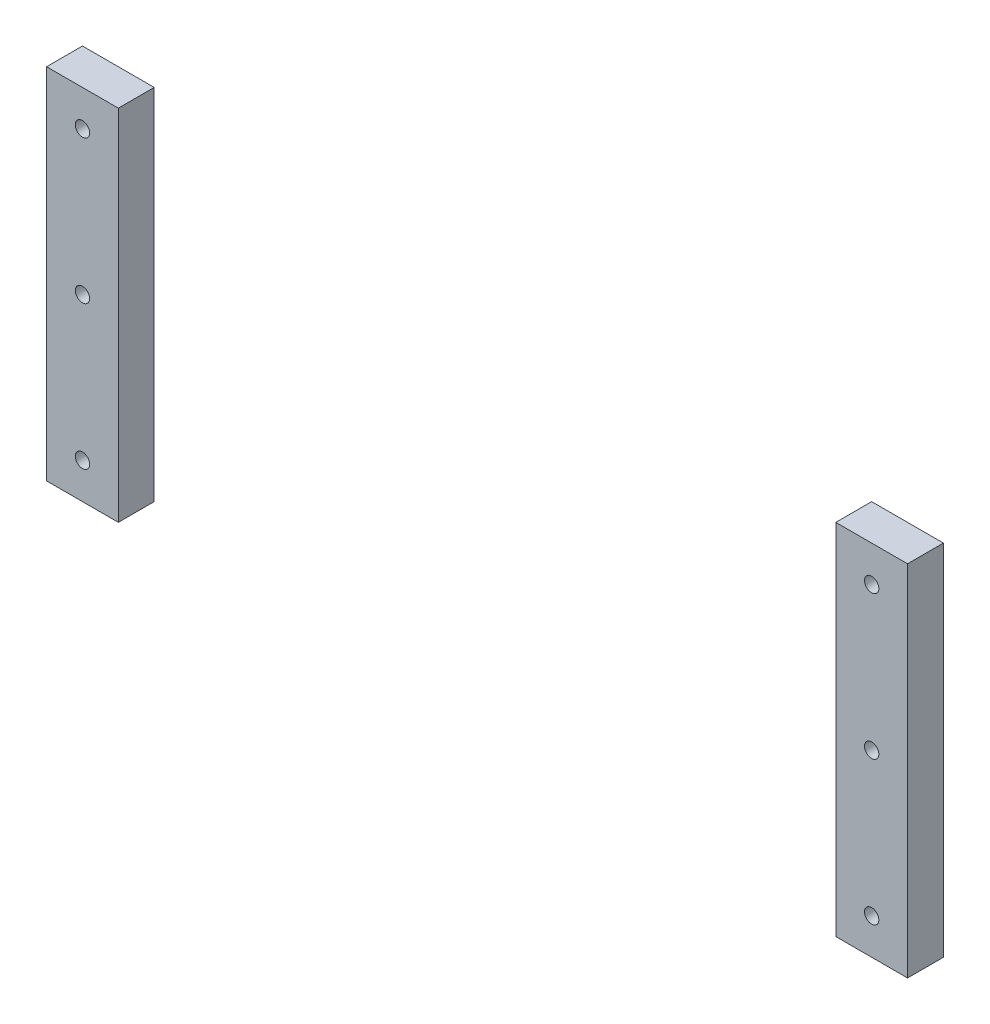
SolidWorks part; units mm, degrees
material "Cast Alloy Steel"
ref_plane "Front Plane" through (0, 0, 0) normal (0, 0, 1) x (1, 0, 0)
ref_plane "Top Plane" through (0, 0, 0) normal (0, 1, 0) x (1, 0, 0)
ref_plane "Right Plane" through (0, 0, 0) normal (1, 0, 0) x (0, 0, -1)
sketch "Sketch1" plane through (0, 0, 0) normal (0, 0, 1) x (1, 0, 0)
  line L0 (200, 0) -> (220, 0)
  line L1 (-20, 0) -> (0, 0)
  line L2 (-20, 0) -> (-20, 100)
  line L3 (-20, 100) -> (0, 100)
  line L4 (0, 0) -> (0, 100)
  line L5 (200, 0) -> (200, 100)
  line L6 (200, 100) -> (220, 100)
  line L7 (220, 0) -> (220, 100)
  line L8 (0, 100) -> (200, 100) construction
  point P4 (0, 0)
  point P11 (0, 0)
  dimension "D1" = 100
  dimension "D2" = 20
  dimension "D3" = 200
extrude "SupportExtrude" add sketch "Sketch1" along normal blind 10
ref_plane "Support Midplane" through (100, 0, 0) normal (1, 0, 0) x (0, 0, -1)
sketch "Sketch2" plane through (0, 0, 10) normal (0, 0, 1) x (1, 0, 0)
  line L0 (-20, 50) -> (0, 50) construction
  line L1 (-20, 100) -> (-20, 0) construction
  line L2 (0, 0) -> (0, 100) construction
  line L3 (-10, 100) -> (-10, 0) construction
  line L4 (0, 100) -> (-20, 100) construction
  line L5 (-20, 0) -> (0, 0) construction
  line L6 (-20, 10) -> (0, 10) construction
  line L7 (-20, 90) -> (0, 90) construction
  line L8 (100, -5.5) -> (100, 5.5) construction
  circle A1 centre (-10, 10) radius 2
  circle A2 centre (-10, 50) radius 2
  circle A3 centre (-10, 90) radius 2
  circle A4 centre (210, 10) radius 2
  circle A5 centre (210, 50) radius 2
  circle A6 centre (210, 90) radius 2
  point P22 (-10, 90)
  point P23 (0, 0)
  dimension "D1" = 10
  dimension "D2" = 4
  dimension "D3" = 10
extrude "Cut-Extrude1" cut sketch "Sketch2" against normal through all
